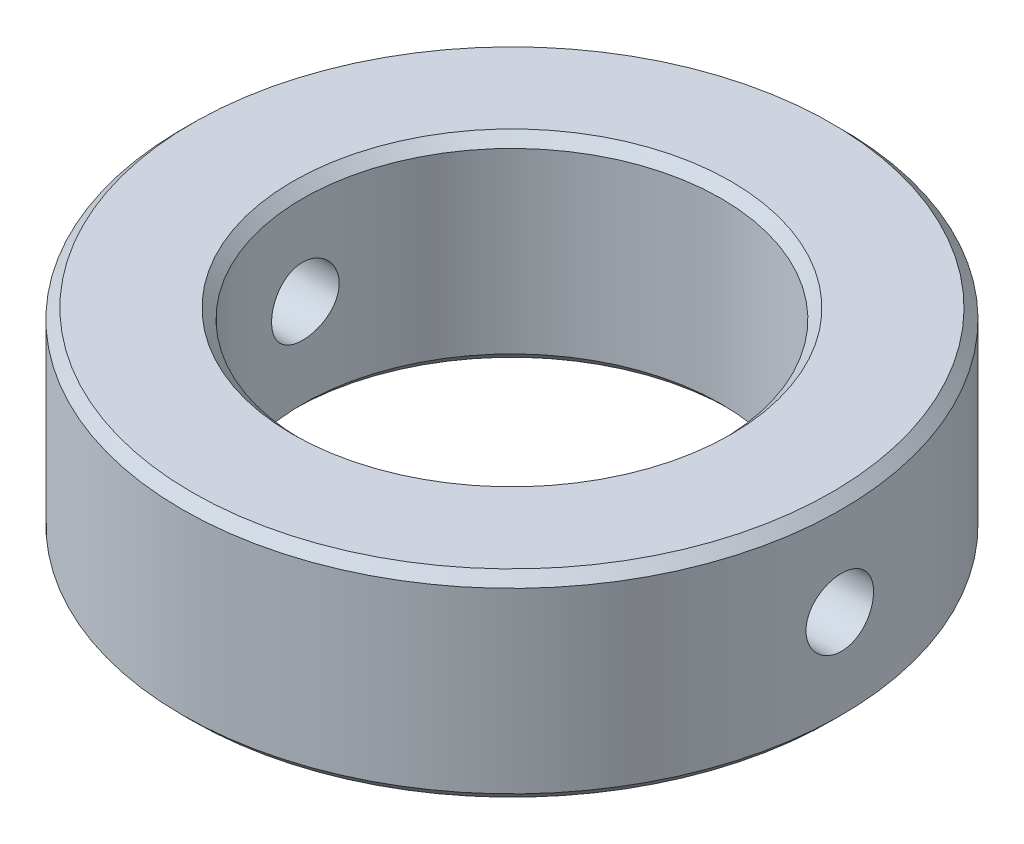
SolidWorks part; units mm, degrees
ref_plane "Front Plane" through (0, 0, 0) normal (0, 0, 1) x (1, 0, 0)
ref_plane "Top Plane" through (0, 0, 0) normal (0, 1, 0) x (1, 0, 0)
ref_plane "Right Plane" through (0, 0, 0) normal (1, 0, 0) x (0, 0, -1)
sketch "Sketch1" plane through (0, 0, 0) normal (0, 1, 0) x (1, 0, 0)
  circle A0 centre (0, 0) radius 10
  circle A1 centre (0, 0) radius 6.35
  dimension "D1" = 20
  dimension "D2" = 12.7
extrude "Boss-Extrude1" add sketch "Sketch1" along normal blind 6
ref_plane "Plane1" through (10, 0, 0) normal (1, 0, 0) x (0, 0, -1)
sketch "Sketch2" plane through (10, 0, 0) normal (1, 0, 0) x (0, 0, -1)
  line L0 (0, 4.0748) -> (0, 1.9555) construction
  line L1 (-3.1185, 3) -> (2.3919, 3) construction
  line L2 (6.35, 6) -> (-6.35, 6) construction
  dimension "D1" = 3
hole_wizard "M2.5x0.45 Tapped Hole1" positions "Sketch3" profile "Sketch4" tap size "M2.5x0.45" standard "ANSI Metric" end condition through all
sketch "Sketch3" plane through (10, 0, 0) normal (1, 0, 0) x (0, 0, -1)
  line L0 (0, 4.0748) -> (0, 1.9555) construction
  line L1 (-3.1185, 3) -> (2.3919, 3) construction
  point P0 (0, 3)
sketch "Sketch4" plane through (10, 3, 0) normal (0, 1, 0) x (0, 0, -1)
  line L0 (0, 0) -> (0, 20)
  line L1 (0, 20) -> (1.025, 20)
  line L2 (1.025, 20) -> (1.025, 0)
  line L5 (1.025, 0) -> (0, 0)
  line L11 (0, -6.35) -> (0, 107.95) construction
  dimension "Thru Tap Drill Dia." = 2.05
  dimension "Thru Tap Drill Depth" = 20
cosmetic thread "Hole Thread1" parameters "D2"=2.5
chamfer "Chamfer1" distance 0.3 angle 45 4 edges at (0, 0, 6.35) (0, 0, 10) (0, 6, 10) (0, 6, 6.35)
